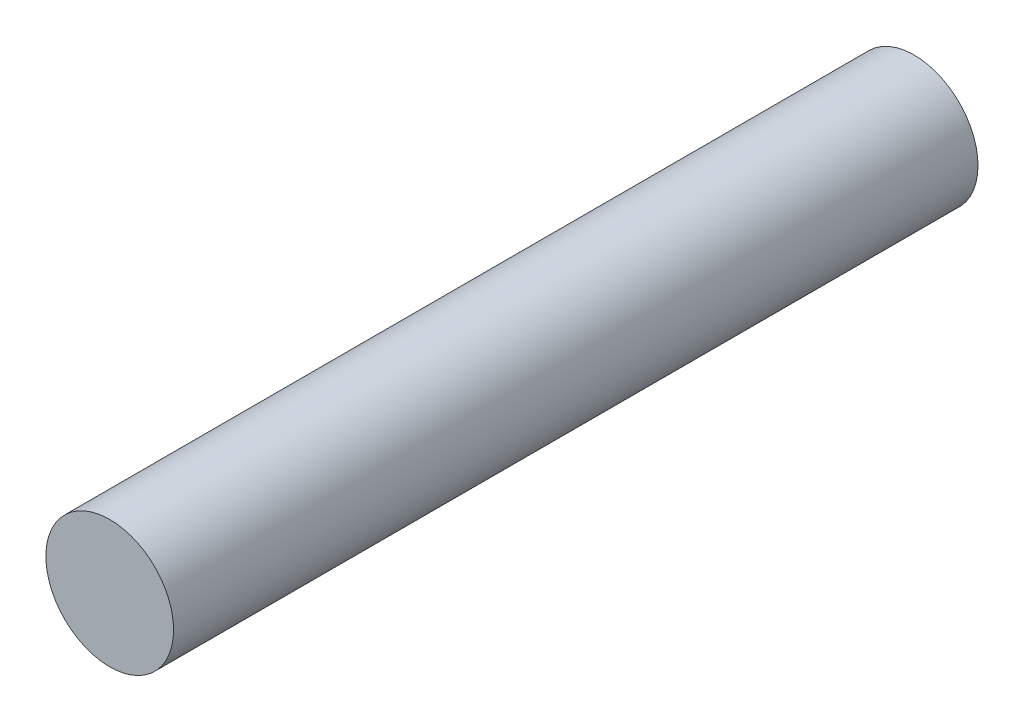
SolidWorks part; units mm, degrees
ref_plane "Front Plane" through (0, 0, 0) normal (0, 0, 1) x (1, 0, 0)
ref_plane "Top Plane" through (0, 0, 0) normal (0, 1, 0) x (1, 0, 0)
ref_plane "Right Plane" through (0, 0, 0) normal (1, 0, 0) x (0, 0, -1)
sketch "Sketch1" plane through (0, 0, 0) normal (0, 0, 1) x (1, 0, 0)
  circle A0 centre (0, 0) radius 1.5875
  dimension "D1" = 3.175
extrude "Boss-Extrude1" add sketch "Sketch1" along normal blind 20
